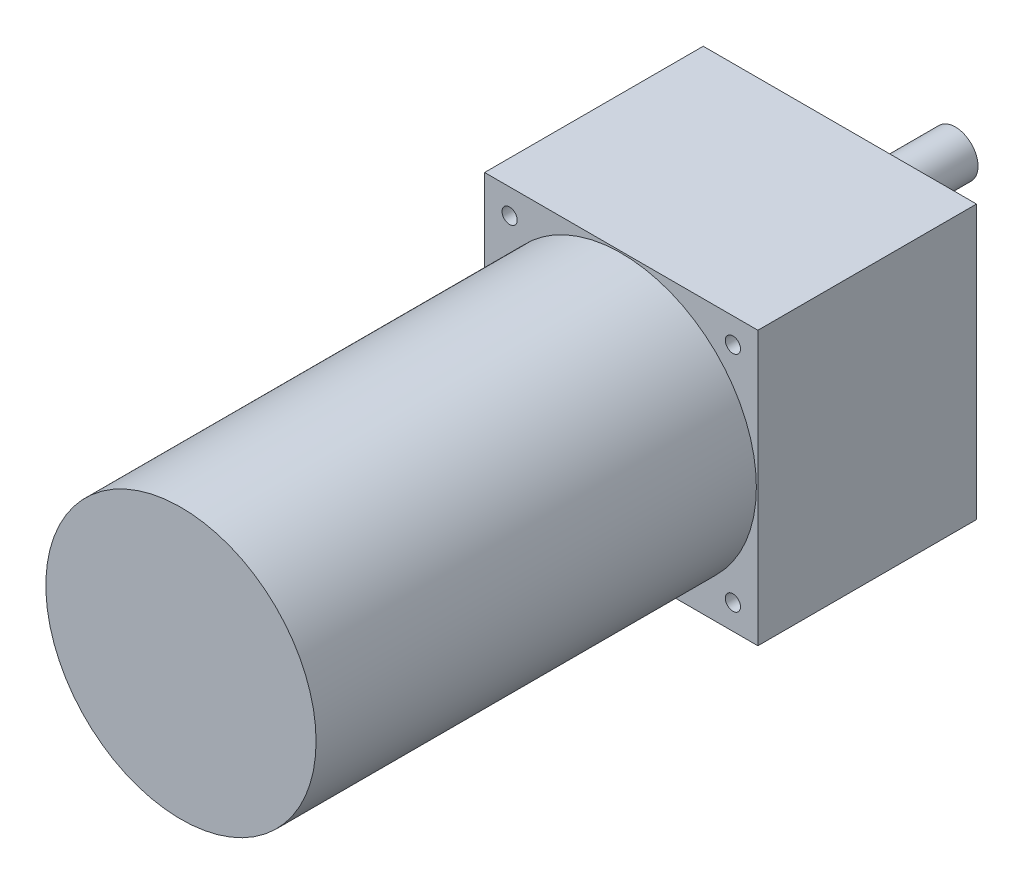
SolidWorks part; units mm, degrees
ref_plane "前视基准面" through (0, 0, 0) normal (0, 0, 1) x (1, 0, 0)
ref_plane "上视基准面" through (0, 0, 0) normal (0, 1, 0) x (1, 0, 0)
ref_plane "右视基准面" through (0, 0, 0) normal (1, 0, 0) x (0, 0, -1)
sketch "草图2" plane through (0, 0, 0) normal (0, 0, 1) x (1, 0, 0)
  line L1 (-45, 45) -> (45, 45)
  line L2 (-45, 45) -> (-45, -45)
  line L3 (-45, -45) -> (45, -45)
  line L4 (45, 45) -> (45, -45)
  line L5 (-45, 45) -> (45, -45) construction
  line L6 (-45, -45) -> (45, 45) construction
  point P0 (0, 0)
  dimension "D1" = 90
  dimension "D2" = 90
extrude "凸台-拉伸1" add sketch "草图2" along normal blind 7
sketch "草图3" plane through (0, 0, 7) normal (0, 0, 1) x (1, 0, 0)
  circle A0 centre (0, 0) radius 44.5
  dimension "D1" = 89
extrude "凸台-拉伸2" add sketch "草图3" along normal blind 145
sketch "草图4" plane through (0, 0, 0) normal (0, 0, -1) x (-1, 0, 0)
  line L1 (-45, 45) -> (45, 45)
  line L2 (-45, 45) -> (-45, -45)
  line L3 (-45, -45) -> (45, -45)
  line L4 (45, 45) -> (45, -45)
  line L5 (-45, 45) -> (45, -45) construction
  line L6 (-45, -45) -> (45, 45) construction
  point P0 (0, 0)
extrude "凸台-拉伸3" add sketch "草图4" along normal blind 65
sketch "草图6" plane through (0, 0, -65) normal (0, 0, -1) x (-1, 0, 0)
  circle A0 centre (0, 18) radius 7.5
  point P3 (0, 0)
  point P4 (-2.3569, 24.6963)
  point P9 (-109.8336, 87.5528)
  point P10 (-137.5964, 101.376)
  dimension "D1" = 15
  dimension "D2" = 18
  dimension "D3" = 0
extrude "凸台-拉伸4" add sketch "草图6" along normal blind 38
sketch "草图7" plane through (0, 0, -65) normal (0, 0, -1) x (-1, 0, 0)
  circle A0 centre (0, 0) radius 52
  point P3 (36.7696, 36.7696)
  point P4 (-36.7696, 36.7696)
  point P5 (-36.7696, -36.7696)
  point P6 (36.7696, -36.7696)
  point P7 (37.9053, 35.5976)
  point P8 (36.7696, 36.7696)
  dimension "D1" = 104
  dimension "D2" = 0
hole_wizard "M6 螺纹孔1" positions "3D草图1" profile "草图8" tap size "M6" standard "GB" end condition through all
sketch3d "3D草图1"
  point P0 (36.7696, 36.7696, -65)
  point P3 (-36.7696, 36.7696, -65)
  point P6 (-36.7696, -36.7696, -65)
  point P9 (36.7696, -36.7696, -65)
cosmetic thread "孔螺蚊线1" parameters "D2"=6
cosmetic thread "孔螺蚊线2" parameters "D2"=6
cosmetic thread "孔螺蚊线3" parameters "D2"=6
cosmetic thread "孔螺蚊线4" parameters "D2"=6
sketch "草图8" plane through (36.7696, 36.7696, -65) normal (1, 0, 0) x (0, 1, 0)
  line L0 (0, 0) -> (0, 217)
  line L1 (0, 217) -> (2.5, 217)
  line L2 (2.5, 217) -> (2.5, 0)
  line L5 (2.5, 0) -> (0, 0)
  line L11 (0, -6.35) -> (0, 107.95) construction
  dimension "通孔螺纹孔钻头直径" = 5
  dimension "通孔螺纹孔钻头深度" = 217
